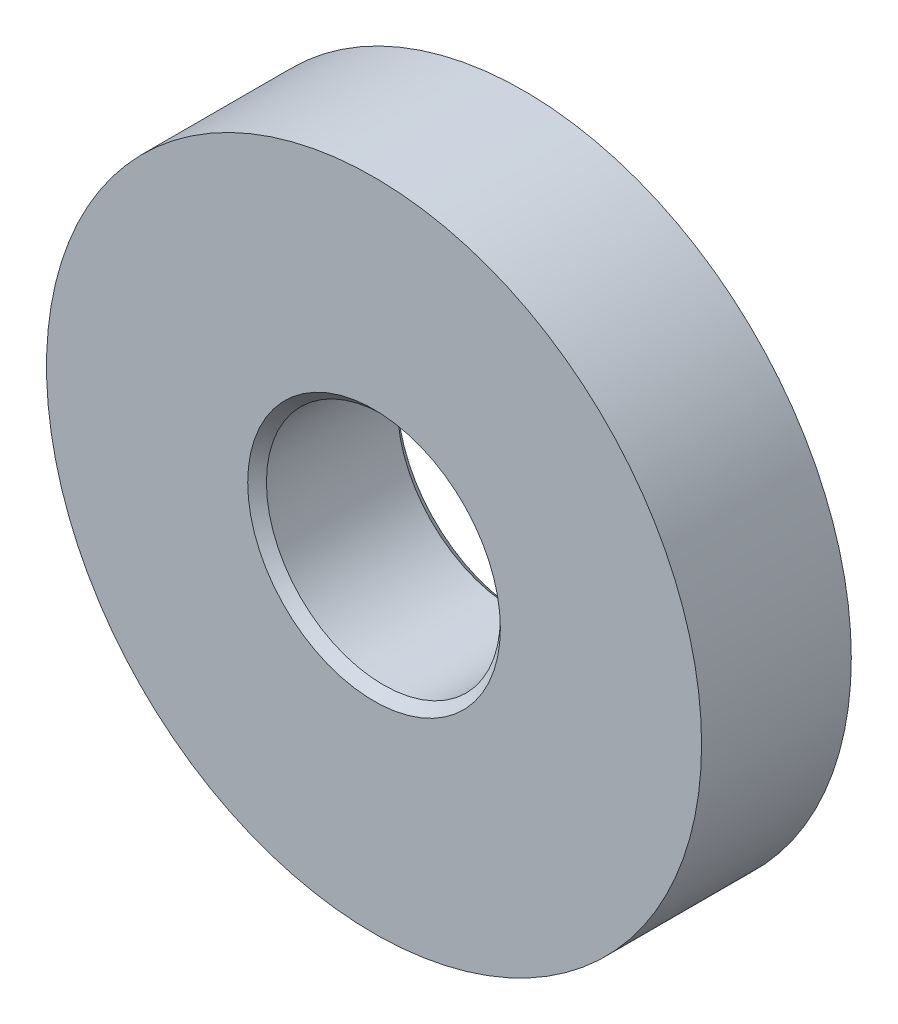
SolidWorks part; units mm, degrees
ref_plane "Front Plane" through (0, 0, 0) normal (0, 0, 1) x (1, 0, 0)
ref_plane "Top Plane" through (0, 0, 0) normal (0, 1, 0) x (1, 0, 0)
ref_plane "Right Plane" through (0, 0, 0) normal (1, 0, 0) x (0, 0, -1)
sketch "Sketch1" plane through (0, 0, 0) normal (0, 0, 1) x (1, 0, 0)
  circle A0 centre (0, 0) radius 3.5
  dimension "D1" = 7
extrude "Boss-Extrude1" add sketch "Sketch1" against normal blind 1.6
sketch "Sketch2" plane through (0, 0, 0) normal (0, 0, 1) x (1, 0, 0)
  circle A0 centre (0, 0) radius 1.25
  dimension "D1" = 2.5
extrude "Cut-Extrude1" cut sketch "Sketch2" against normal through all
chamfer "Chamfer1" distance 0.1 angle 45 2 edges at (1.25, 0, -1.6) (1.25, 0, 0)
